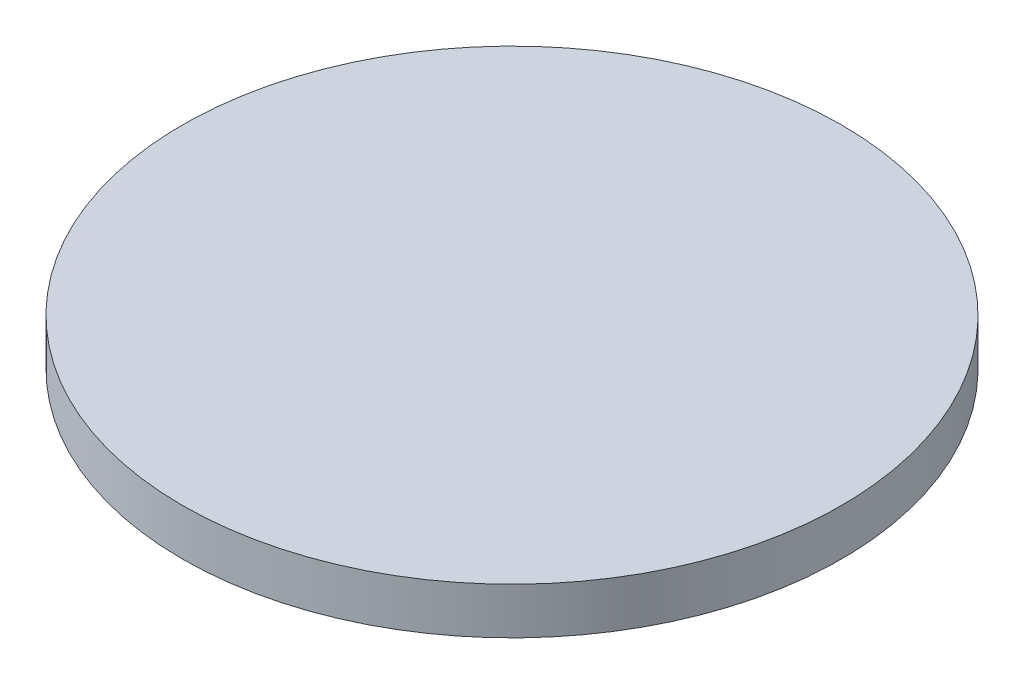
SolidWorks part; units mm, degrees
ref_plane "Front Plane" through (0, 0, 0) normal (0, 0, 1) x (1, 0, 0)
ref_plane "Top Plane" through (0, 0, 0) normal (0, 1, 0) x (1, 0, 0)
ref_plane "Right Plane" through (0, 0, 0) normal (1, 0, 0) x (0, 0, -1)
sketch "Sketch1" plane through (0, 0, 0) normal (0, 1, 0) x (1, 0, 0)
  circle A0 centre (0, 0) radius 113.5
extrude "Boss-Extrude1" add sketch "Sketch1" along normal blind 16
